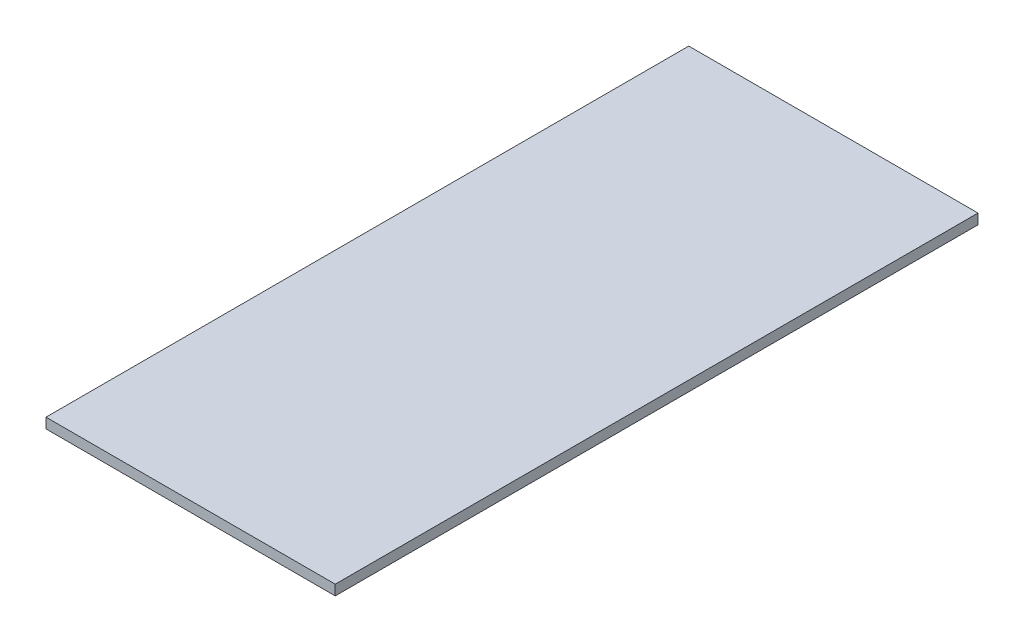
SolidWorks part; units mm, degrees
ref_plane "Front Plane" through (0, 0, 0) normal (0, 0, 1) x (1, 0, 0)
ref_plane "Top Plane" through (0, 0, 0) normal (0, 1, 0) x (1, 0, 0)
ref_plane "Right Plane" through (0, 0, 0) normal (1, 0, 0) x (0, 0, -1)
sketch "Sketch1" plane through (0, 0, 0) normal (0, 1, 0) x (1, 0, 0)
  line L1 (0, 0) -> (90, 0)
  line L2 (0, 0) -> (0, 200)
  line L3 (0, 200) -> (90, 200)
  line L4 (90, 0) -> (90, 200)
  dimension "D1" = 90
  dimension "D2" = 200
extrude "Boss-Extrude1" add sketch "Sketch1" along normal blind 3.175
